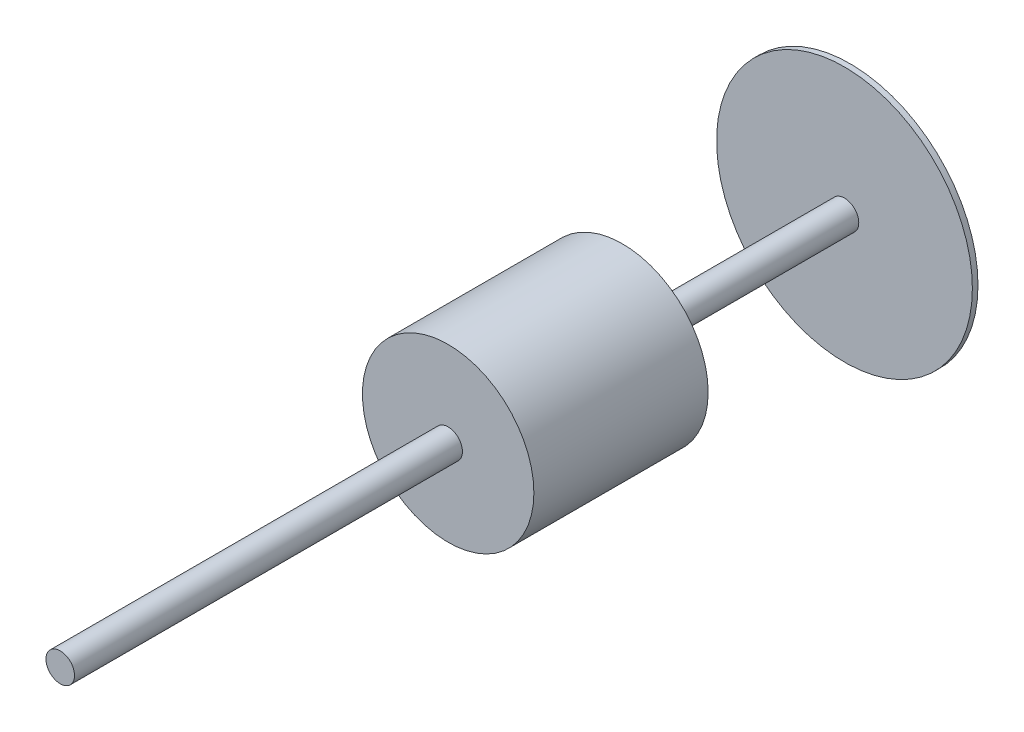
SolidWorks part; units mm, degrees
other "Markup1"
sketch "Sketch6" plane through (500, -500, -1363.6) normal (1, 0, 0) x (0, 0, -1)
ref_plane "Top Plane" through (0, 0, 0) normal (0, 0, 1) x (1, 0, 0)
ref_plane "Right Plane" through (0, 0, 0) normal (0, 1, 0) x (1, 0, 0)
ref_plane "Front Plane" through (0, 0, 0) normal (1, 0, 0) x (0, 0, -1)
sketch "Sketch1" plane through (0, 0, 0) normal (0, 0, 1) x (1, 0, 0)
  circle A0 centre (0, 0) radius 50.8
  dimension "D1" = 101.6
extrude "Boss-Extrude1" add sketch "Sketch1" against normal blind 680 and the other way blind 2130
sketch "Sketch2" plane through (0, 0, -680) normal (0, 0, 1) x (1, 0, 0)
  circle A0 centre (0, 0) radius 455
  dimension "D1" = 910
extrude "Boss-Extrude2" add sketch "Sketch2" along normal blind 20
sketch "Sketch3" plane through (0, 0, -660) normal (0, 0, 1) x (1, 0, 0)
  circle A0 centre (0, 0) radius 222.25
  dimension "D1" = 444.5
sketch "Sketch7" plane through (0, 0, 2130) normal (0, 0, 1) x (1, 0, 0)
  circle A0 centre (0, 0) radius 305
extrude "Boss-Extrude3" add sketch "Sketch7" along a picked direction on the side against the normal blind 620 from offset 1380 offset against normal yes
sketch "Sketch8" plane through (0, 0, 130) normal (0, 0, -1) x (-1, 0, 0)
  circle A0 centre (0, 0) radius 225
extrude "Boss-Extrude4" add sketch "Sketch8" along normal blind 50
